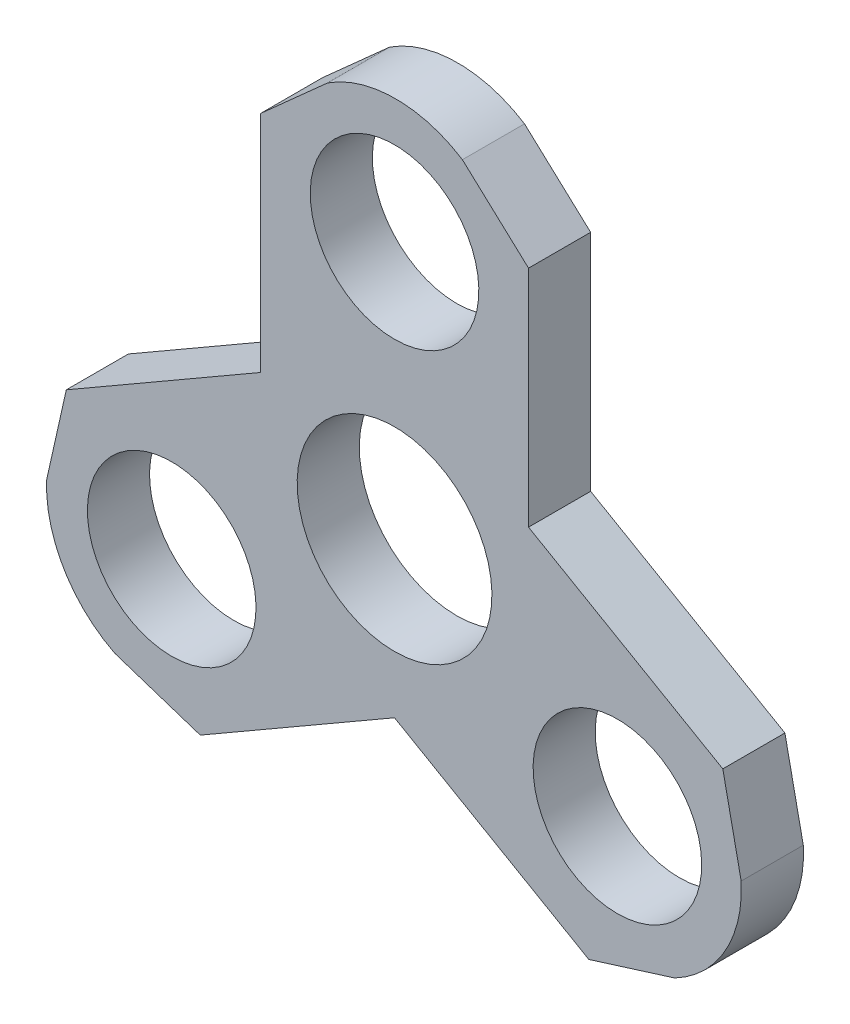
SolidWorks part; units mm, degrees
ref_plane "Front Plane" through (0, 0, 0) normal (0, 0, 1) x (1, 0, 0)
ref_plane "Top Plane" through (0, 0, 0) normal (0, 1, 0) x (1, 0, 0)
ref_plane "Right Plane" through (0, 0, 0) normal (1, 0, 0) x (0, 0, -1)
sketch "Sketch2" plane through (0, 0, 0) normal (0, 1, 0) x (1, 0, 0)
  line L2 (15.1, 8.718) -> (15.1, 34)
  line L3 (-15.1, 8.718) -> (-15.1, 34)
  line L4 (-15.1, 34) -> (-7.5481, 40.7517)
  line L5 (15.1, 34) -> (7.6467, 40.8604)
  line L6 (36.9949, -3.923) -> (39.0661, -13.839)
  line L7 (21.8949, -30.077) -> (31.5628, -27.0524)
  line L8 (0, -17.436) -> (21.8949, -30.077)
  line L9 (15.1, 8.718) -> (36.9949, -3.923)
  line L10 (-21.8949, -30.077) -> (-31.518, -26.9127)
  line L11 (-36.9949, -3.923) -> (-39.2095, -13.808)
  line L12 (-15.1, 8.718) -> (-36.9949, -3.923)
  line L13 (0, -17.436) -> (-21.8949, -30.077)
  circle A0 centre (0, 0) radius 10.975
  circle A2 centre (0, 29) radius 9.5
  arc A3 (-7.5481, 40.7517) -> (7.6467, 40.8604) centre (0.1334, 29.0472) cw
  arc A4 (39.0661, -13.839) -> (31.5628, -27.0524) centre (25.0889, -14.6392) cw
  circle A5 centre (25.1147, -14.5) radius 9.5
  arc A6 (-31.518, -26.9127) -> (-39.2095, -13.808) centre (-25.2224, -14.4081) cw
  circle A7 centre (-25.1147, -14.5) radius 9.5
  point P6 (0, 0)
  point P38 (0, 0)
  dimension "D3" = 21.95
  dimension "D8" = 19
  dimension "D11" = 3
  dimension "D2" = 14
  dimension "D9" = 10.13
  dimension "D10" = 10.13
extrude "Boss-Extrude1" add sketch "Sketch2" along normal blind 7
move or copy body "Body-Move/Copy2" bodies to move or copy 101 copy no rotation origin (0, 3.5, -6.4851) rotation axis (1, 0, 0) rotation angle 90
